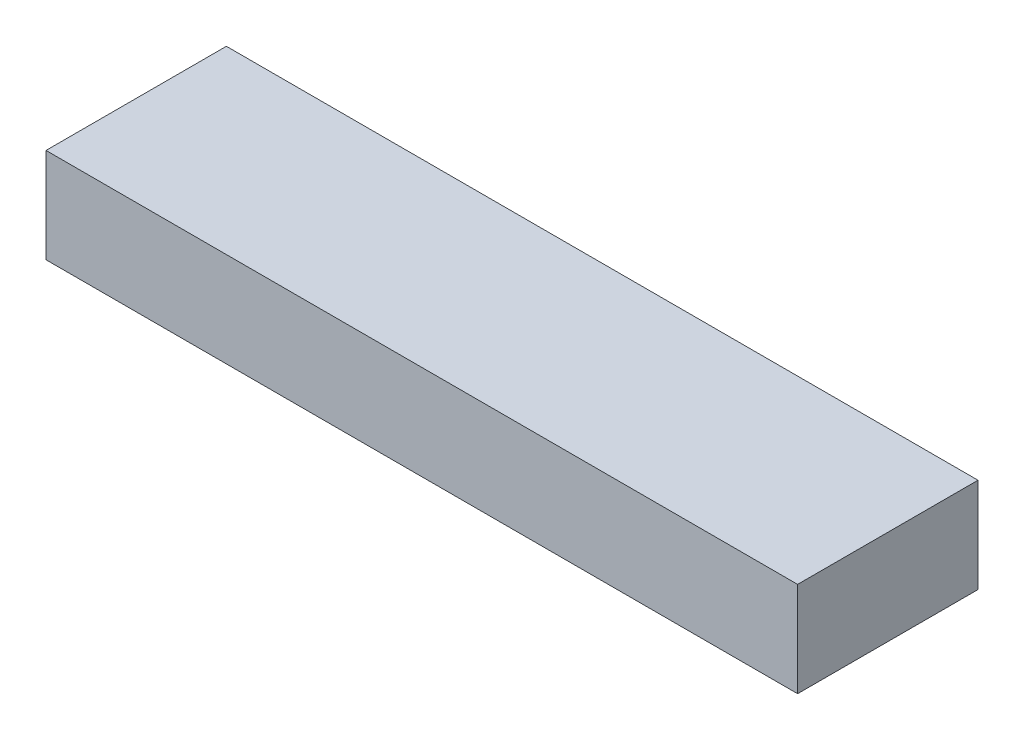
SolidWorks part; units mm, degrees
ref_plane "Front Plane" through (0, 0, 0) normal (0, 0, 1) x (1, 0, 0)
ref_plane "Top Plane" through (0, 0, 0) normal (0, 1, 0) x (1, 0, 0)
ref_plane "Right Plane" through (0, 0, 0) normal (1, 0, 0) x (0, 0, -1)
sketch "Sketch1" plane through (0, 0, 0) normal (0, 1, 0) x (1, 0, 0)
  line L1 (-12.5, 3) -> (12.5, 3)
  line L2 (-12.5, 3) -> (-12.5, -3)
  line L3 (-12.5, -3) -> (12.5, -3)
  line L4 (12.5, 3) -> (12.5, -3)
  line L5 (-12.5, 3) -> (12.5, -3) construction
  line L6 (-12.5, -3) -> (12.5, 3) construction
  point P0 (0, 0)
  dimension "D1" = 25
  dimension "D2" = 6
extrude "Boss-Extrude1" add sketch "Sketch1" along normal blind 3.15
sketch "Sketch2" plane through (0, 3.15, 0) normal (0, 1, 0) x (1, 0, 0)
  line L0 (0, -3) -> (0, 3) construction
  line L1 (-12.5, -3) -> (12.5, -3) construction
  line L2 (12.5, 3) -> (-12.5, 3) construction
  line L3 (12.5, 0) -> (-12.5, 0) construction
  line L4 (12.5, -3) -> (12.5, 3) construction
  line L5 (-12.5, 3) -> (-12.5, -3) construction
